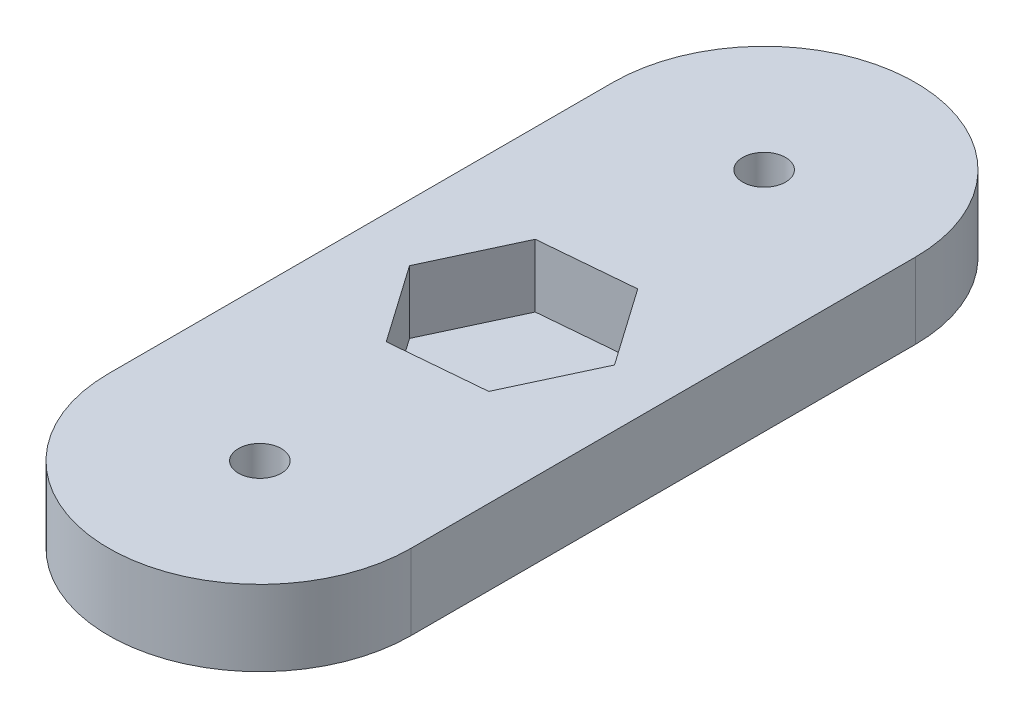
SolidWorks part; units mm, degrees
material "ABS PC"
ref_plane "Front Plane" through (0, 0, 0) normal (0, 0, 1) x (1, 0, 0)
ref_plane "Top Plane" through (0, 0, 0) normal (0, 1, 0) x (1, 0, 0)
ref_plane "Right Plane" through (0, 0, 0) normal (1, 0, 0) x (0, 0, -1)
sketch "Sketch1" plane through (0, 0, 0) normal (0, 1, 0) x (1, 0, 0)
  line L0 (0, 0) -> (0, 40) construction
  line L1 (-12, 0) -> (-12, 40)
  line L2 (12, 0) -> (12, 40)
  arc A0 (-12, 0) -> (12, 0) centre (0, 0) ccw
  arc A1 (12, 40) -> (-12, 40) centre (0, 40) ccw
  circle A2 centre (0, 40) radius 1.7
  circle A3 centre (0, 0) radius 1.7
  point P3 (0, 20)
  dimension "D2" = 40
  dimension "D3" = 3.4
  dimension "D1" = 24
extrude "Boss-Extrude1" add sketch "Sketch1" along normal blind 6
sketch "Sketch2" plane through (0, 6, 0) normal (0, 1, 0) x (1, 0, 0)
  line L0 (12, 0) -> (12, 40) construction
  line L1 (4.305, 13.8518) -> (7.477, 20.6542)
  line L2 (7.477, 20.6542) -> (3.172, 26.8023)
  line L3 (3.172, 26.8023) -> (-4.305, 26.1482)
  line L4 (-4.305, 26.1482) -> (-7.477, 19.3458)
  line L5 (-7.477, 19.3458) -> (-3.172, 13.1977)
  line L6 (-3.172, 13.1977) -> (4.305, 13.8518)
  line L7 (-12, 40) -> (-12, 0) construction
  circle A0 centre (0, 20) radius 6.5 construction
  dimension "D1" = 13
  dimension "D2" = 12
  dimension "D3" = 20
  dimension "D4" = 95
extrude "Cut-Extrude1" cut sketch "Sketch2" against normal blind 5
